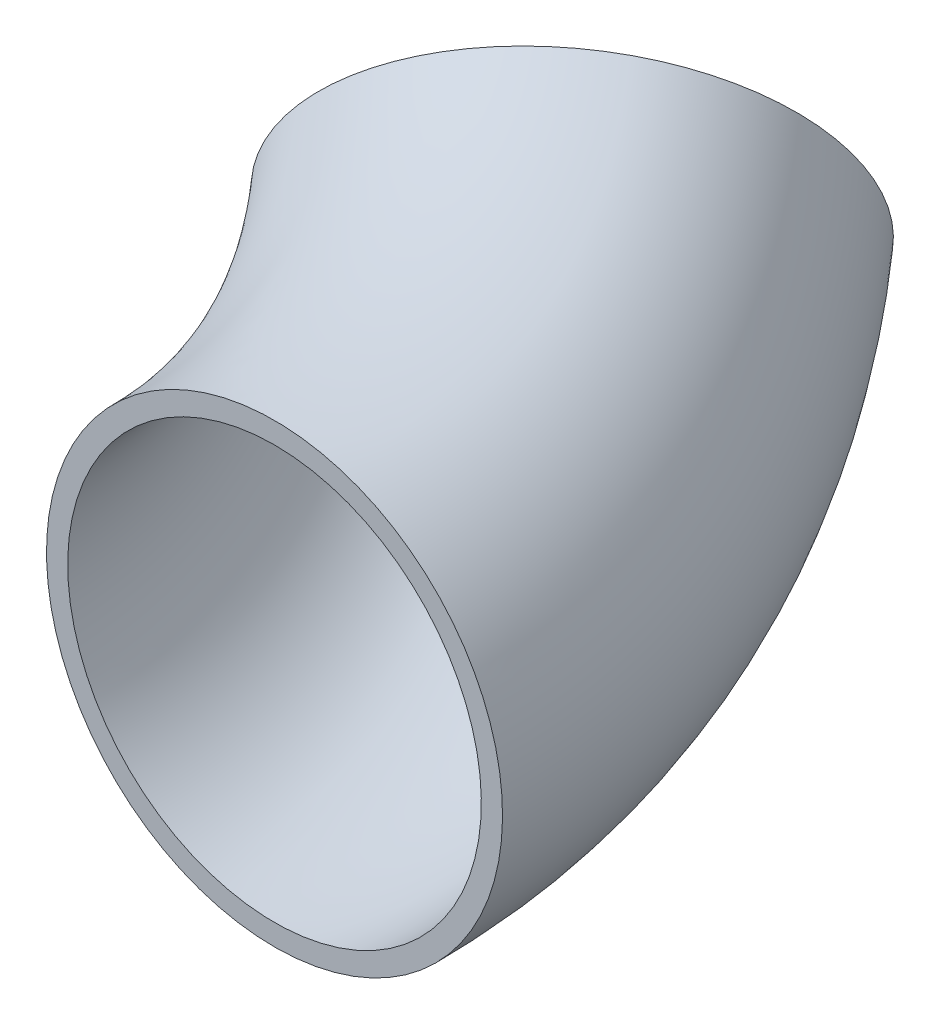
SolidWorks part; units mm, degrees
ref_plane "Front" through (0, 0, 0) normal (0, 0, 1) x (1, 0, 0)
ref_plane "Top" through (0, 0, 0) normal (0, 1, 0) x (1, 0, 0)
ref_plane "Side" through (0, 0, 0) normal (1, 0, 0) x (0, 0, -1)
sketch "FilterSketch" plane through (0, 0, 0) normal (0, 0, 1) x (1, 0, 0)
  circle A0 centre (0, 0) radius 127 construction
  dimension "NominalDiameter" = 254
sketch3d "3DSketch1"
  arc A0 (0, 0, 0) -> (-91.1147, 64.4279, -269.4077) centre (-311.0852, 219.9705, 0) ccw construction
  arc A1 (0, 0, 0) -> (-91.1147, 64.4279, -269.4077) centre (-311.0852, 219.9705, 0) ccw
  point P3 (-91.1147, 531.0556, 0)
  point P4 (-91.1147, 531.0556, 0)
sketch "PipeSketch" plane through (0, 0, 0) normal (0, 0, 1) x (1, 0, 0)
  circle A0 centre (0, 0) radius 136.525
  circle A1 centre (0, 0) radius 123.825 construction
  dimension "OuterDiameter" = 273.05
  dimension "InnerDiameter" = 247.65
sweep "Sweep-Thin1" add profiles "PipeSketch" path "3DSketch1" parameters "D1"=12.7
